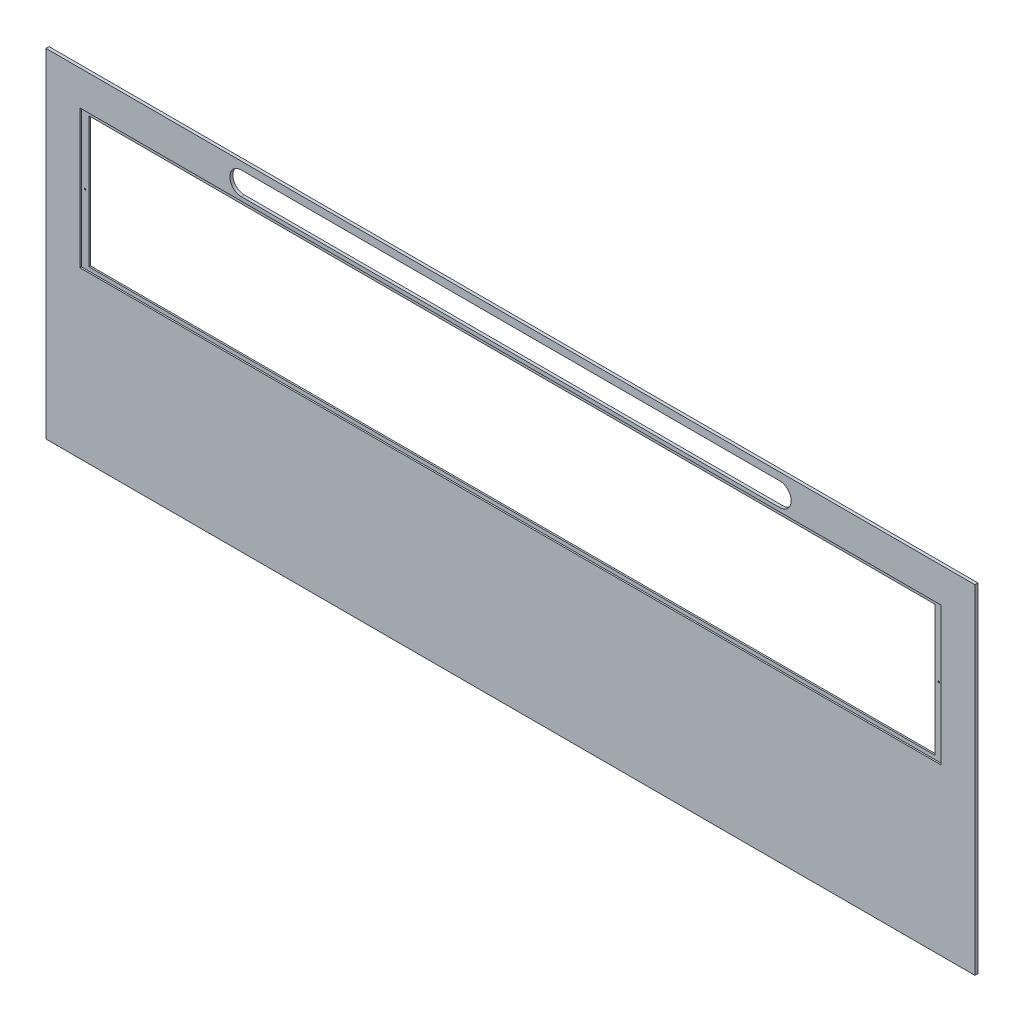
SolidWorks part; units mm, degrees
material "PVC Rigid"
ref_plane "Front Plane" through (0, 0, 0) normal (0, 0, 1) x (1, 0, 0)
ref_plane "Top Plane" through (0, 0, 0) normal (0, 1, 0) x (1, 0, 0)
ref_plane "Right Plane" through (0, 0, 0) normal (1, 0, 0) x (0, 0, -1)
sketch "Sketch1" plane through (0, 0, 0) normal (0, 0, 1) x (1, 0, 0)
  line L1 (-604, -220) -> (604, -220)
  line L2 (-604, -220) -> (-604, 220)
  line L3 (-604, 220) -> (604, 220)
  line L4 (604, -220) -> (604, 220)
  line L5 (-604, -220) -> (604, 220) construction
  line L6 (-604, 220) -> (604, -220) construction
  point P0 (0, 0)
extrude "Boss-Extrude1" add sketch "Sketch1" along normal blind 4
sketch "Sketch2" plane through (0, 0, 4) normal (0, 0, 1) x (1, 0, 0)
  line L2 (-350, 210) -> (350, 210)
  line L3 (-350, 180) -> (350, 180)
  arc A0 (-350, 210) -> (-350, 180) centre (-350, 195) ccw
  arc A1 (350, 210) -> (350, 180) centre (350, 195) cw
extrude "Cut-Extrude1" cut sketch "Sketch2" against normal blind 10
sketch "Sketch3" plane through (0, 0, 4) normal (0, 0, 1) x (1, 0, 0)
  line L0 (0, 220) -> (0, 175) construction
  line L1 (604, 220) -> (-604, 220) construction
  line L2 (-560, 175) -> (560, 175)
  line L3 (-560, 175) -> (-560, -5)
  line L4 (-560, -5) -> (560, -5)
  line L5 (560, -5) -> (560, 175)
  point P7 (0, 175)
extrude "Cut-Extrude2" cut sketch "Sketch3" against normal blind 2
sketch "Sketch4" plane through (0, 0, 2) normal (0, 0, 1) x (1, 0, 0)
  line L0 (0, 175) -> (0, 170) construction
  line L1 (560, 175) -> (-560, 175) construction
  line L2 (-550, 170) -> (550, 170)
  line L3 (-550, 170) -> (-550, 0)
  line L4 (-550, 0) -> (550, 0)
  line L5 (550, 0) -> (550, 170)
  point P7 (0, 170)
extrude "Cut-Extrude3" cut sketch "Sketch4" against normal through all
sketch "Sketch5" plane through (0, 0, 2) normal (0, 0, 1) x (1, 0, 0)
  line L0 (-550, 170) -> (-550, 0) construction
  line L2 (550, 170) -> (-550, 170) construction
  circle A0 centre (-555, 85) radius 1
  dimension "D1" = 5
  dimension "D2" = 85
extrude "Cut-Extrude4" cut sketch "Sketch5" against normal blind 1 contours A0
mirror "Mirror1" about plane through (0, 0, 0) normal (1, 0, 0) of "Cut-Extrude4"
